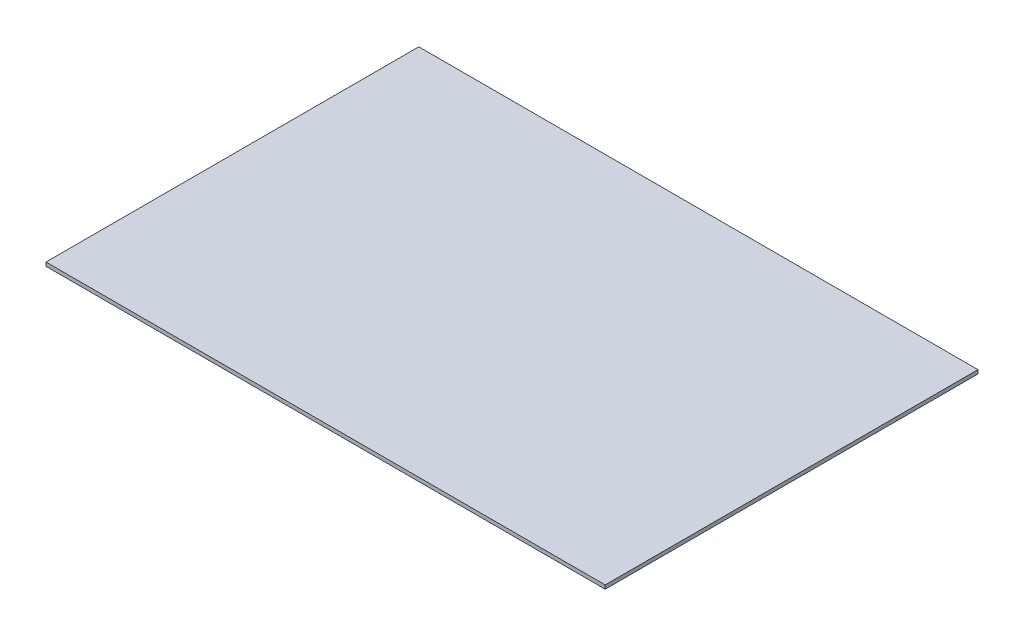
SolidWorks part; units mm, degrees
ref_plane "Front Plane" through (0, 0, 0) normal (0, 0, 1) x (1, 0, 0)
ref_plane "Top Plane" through (0, 0, 0) normal (0, 1, 0) x (1, 0, 0)
ref_plane "Right Plane" through (0, 0, 0) normal (1, 0, 0) x (0, 0, -1)
sketch "Sketch1" plane through (0, 0, 0) normal (0, 1, 0) x (1, 0, 0)
  line L1 (0, 0) -> (-1500, 0)
  line L2 (0, 0) -> (0, 1000)
  line L3 (0, 1000) -> (-1500, 1000)
  line L4 (-1500, 0) -> (-1500, 1000)
  dimension "D1" = 1000
  dimension "D2" = 1500
extrude "Extrude1" add sketch "Sketch1" along normal blind 10
